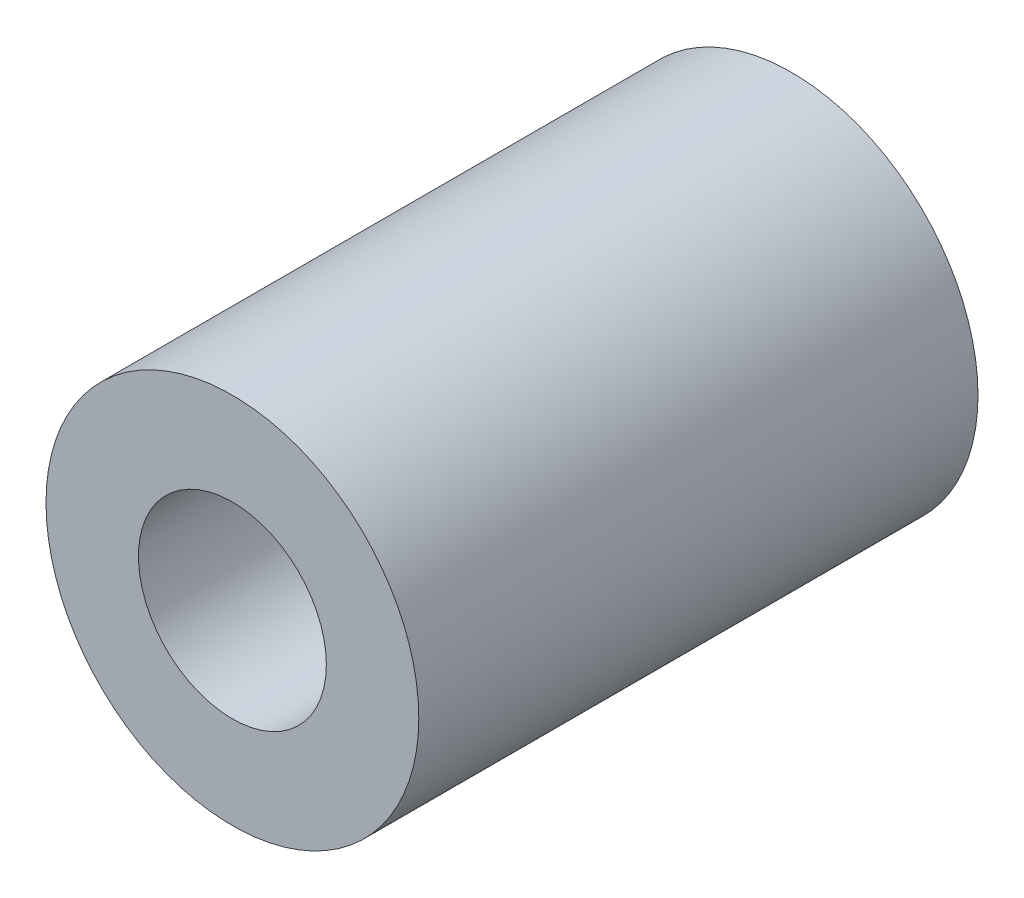
SolidWorks part; units mm, degrees
material "Nylon 101"
ref_plane "Front Plane" through (0, 0, 0) normal (0, 0, 1) x (1, 0, 0)
ref_plane "Top Plane" through (0, 0, 0) normal (0, 1, 0) x (1, 0, 0)
ref_plane "Right Plane" through (0, 0, 0) normal (1, 0, 0) x (0, 0, -1)
sketch "Sketch1" plane through (0, 0, 0) normal (0, 0, 1) x (1, 0, 0)
  line L0 (0, 3.2004) -> (0, 6.35) construction
  line L1 (0, -3.2004) -> (0, -6.35) construction
  circle A0 centre (0, 0) radius 6.35
  circle A1 centre (0, 0) radius 3.2004
  dimension "OD" = 12.7
  dimension "ID" = 6.4008
sketch "Sketch2" plane through (0, 0, 0) normal (1, 0, 0) x (0, 0, -1)
  line L0 (-9.525, 3.2004) -> (9.525, 3.2004) construction
  line L1 (-9.525, -3.2004) -> (9.525, -3.2004) construction
  line L2 (-9.525, -6.35) -> (9.525, -6.35) construction
  line L3 (-9.525, 6.35) -> (9.525, 6.35) construction
  dimension "Length" = 19.05
extrude "Extrude1" add sketch "Sketch1" along normal up to vertex (9.525 mm away) and the other way up to vertex (9.525 mm away) up to point (0, 3.2004, 9.525) other way up to point (0, 3.2004, -9.525)
sketch "Sketch3" plane through (0, 0, 9.525) normal (0, 0, 1) x (1, 0, 0)
  circle A0 centre (0, 0) radius 3.2004 construction
  circle A3 centre (0, 0) radius 3.2004
  point P3 (-3.2004, 0)
